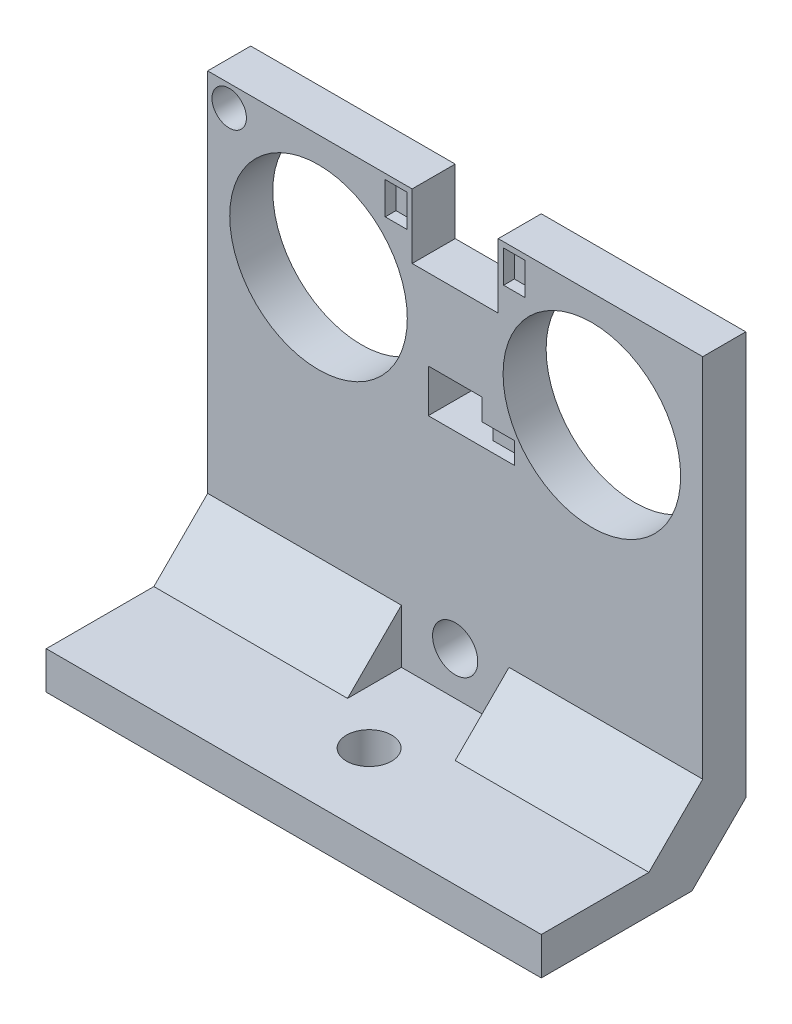
SolidWorks part; units mm, degrees
material "ABS"
ref_plane "前基準面" through (0, 0, 0) normal (0, 0, 1) x (1, 0, 0)
ref_plane "上基準面" through (0, 0, 0) normal (0, 1, 0) x (1, 0, 0)
ref_plane "右基準面" through (0, 0, 0) normal (1, 0, 0) x (0, 0, -1)
sketch "草圖1" plane through (0, 0, 0) normal (0, 0, 1) x (1, 0, 0)
  line L1 (-23, -10) -> (23, -10)
  line L2 (-23, -10) -> (-23, 10)
  line L3 (-23, 10) -> (23, 10)
  line L4 (23, -10) -> (23, 10)
  line L5 (-23, -10) -> (23, 10) construction
  line L6 (-23, 10) -> (23, -10) construction
  point P0 (0, 0)
  dimension "D1" = 46
  dimension "D2" = 20
extrude "填料-伸長1" add sketch "草圖1" along normal blind 4
sketch "草圖2" plane through (0, 0, 4) normal (0, 0, 1) x (1, 0, 0)
  line L0 (-12.7, -0.65) -> (12.7, -0.65) construction
  line L1 (23, 10) -> (-23, 10) construction
  circle A0 centre (-12.7, -0.65) radius 8.25
  circle A1 centre (12.7, -0.65) radius 8.25
  point P4 (0, -0.65)
  dimension "D1" = 25.4
  dimension "D2" = 16.5
  dimension "D3" = 10.65
extrude "除料-伸長1" cut sketch "草圖2" against normal through all
sketch "草圖3" plane through (0, 0, 4) normal (0, 0, 1) x (1, 0, 0)
  line L0 (0, 0) -> (0, 7) construction
  line L1 (23, 10) -> (-23, 10) construction
  line L2 (-4, 4) -> (4, 4)
  line L3 (-4, 4) -> (-4, 10)
  line L4 (-4, 10) -> (4, 10)
  line L5 (4, 4) -> (4, 10)
  line L6 (-4, 4) -> (4, 10) construction
  line L7 (-4, 10) -> (4, 4) construction
  dimension "D1" = 8
  dimension "D2" = 6
extrude "除料-伸長2" cut sketch "草圖3" against normal through all
sketch "草圖4" plane through (0, 0, 4) normal (0, 0, 1) x (1, 0, 0)
  line L0 (0, 0) -> (0, -5.5) construction
  line L2 (-2.5, -3.5) -> (2.5, -3.5)
  line L3 (-2.5, -3.5) -> (-2.5, -7.5)
  line L4 (-2.5, -7.5) -> (2.5, -7.5)
  line L5 (2.5, -3.5) -> (2.5, -7.5)
  line L6 (-2.5, -3.5) -> (2.5, -7.5) construction
  line L7 (-2.5, -7.5) -> (2.5, -3.5) construction
  dimension "D1" = 5
  dimension "D2" = 4
  dimension "D3" = 5.5
extrude "除料-伸長3" cut sketch "草圖4" against normal through all
sketch "草圖5" plane through (0, 0, 4) normal (0, 0, 1) x (1, 0, 0)
  line L0 (0, 0) -> (0, 8) construction
  line L1 (2.5, -7.5) -> (5.5, -7.5)
  line L2 (2.5, -7.5) -> (2.5, -5.5)
  line L3 (2.5, -5.5) -> (5.5, -5.5)
  line L4 (5.5, -7.5) -> (5.5, -5.5)
  line L5 (-5.5, 8) -> (5.5, 8) construction
  line L6 (23, 10) -> (4, 10) construction
  line L7 (-4.5, 9.5) -> (-6.5, 9.5)
  line L8 (-4.5, 9.5) -> (-4.5, 6.5)
  line L9 (-4.5, 6.5) -> (-6.5, 6.5)
  line L10 (-6.5, 9.5) -> (-6.5, 6.5)
  line L11 (-4.5, 9.5) -> (-6.5, 6.5) construction
  line L12 (-4.5, 6.5) -> (-6.5, 9.5) construction
  line L13 (6.5, 9.5) -> (4.5, 9.5)
  line L14 (6.5, 9.5) -> (6.5, 6.5)
  line L15 (6.5, 6.5) -> (4.5, 6.5)
  line L16 (4.5, 9.5) -> (4.5, 6.5)
  line L17 (6.5, 9.5) -> (4.5, 6.5) construction
  line L18 (6.5, 6.5) -> (4.5, 9.5) construction
  point P10 (0, 8)
  dimension "D1" = 2
  dimension "D2" = 3
  dimension "D3" = 2
  dimension "D4" = 3
  dimension "D5" = 11
  dimension "D6" = 0.5
extrude "除料-伸長4" cut sketch "草圖5" against normal blind 1
sketch "草圖6" plane through (0, -10, 0) normal (0, -1, 0) x (1, 0, 0)
  line L1 (-23, 4) -> (23, 4)
  line L2 (-23, 4) -> (-23, 0)
  line L3 (-23, 0) -> (23, 0)
  line L4 (23, 4) -> (23, 0)
extrude "填料-伸長2" add sketch "草圖6" along normal blind 22.5
sketch "草圖8" plane through (-23, 0, 0) normal (-1, 0, 0) x (0, 0, 1)
  line L0 (4, -32.5) -> (19, -32.5)
  line L1 (19, -32.5) -> (19, -29)
  line L2 (19, -29) -> (4, -29)
  line L3 (4, 10) -> (4, -32.5) construction
  line L4 (4, -29) -> (4, -32.5)
  dimension "D1" = 3.5
  dimension "D2" = 15
extrude "填料-伸長4" add sketch "草圖8" against normal blind 46
chamfer "導角3" distance 5 angle 45 2 edges at (0, -32.5, 0) (0, -29, 4)
sketch "草圖9" plane through (0, -29, 0) normal (0, 1, 0) x (1, 0, 0)
  line L0 (0, -4) -> (0, -19) construction
  line L1 (23, -4) -> (-23, -4) construction
  line L2 (23, -19) -> (-23, -19) construction
  circle A0 centre (0, -12) radius 2.1
  dimension "D1" = 4.2
  dimension "D2" = 8
extrude "除料-伸長5" cut sketch "草圖9" against normal through all
sketch "草圖10" plane through (0, 0, 0) normal (0, 0, -1) x (-1, 0, 0)
  line L0 (0, -25) -> (0, -32.5) construction
  line L1 (23, -32.5) -> (-23, -32.5) construction
  circle A0 centre (0, -25) radius 2.1
  dimension "D2" = 4.2
  dimension "D1" = 7.5
extrude "除料-伸長6" cut sketch "草圖10" against normal through all
sketch "草圖13" plane through (0, 0, 4) normal (0, 0, 1) x (1, 0, 0)
  line L0 (23, -29) -> (-23, -29) construction
  line L1 (-5, -21) -> (5, -21)
  line L2 (-5, -21) -> (-5, -29)
  line L3 (-5, -29) -> (5, -29)
  line L4 (5, -21) -> (5, -29)
  line L5 (-5, -21) -> (5, -29) construction
  line L6 (-5, -29) -> (5, -21) construction
  point P0 (0, -25)
  dimension "D1" = 10
extrude "除料-伸長9" cut sketch "草圖13" along normal blind 46
sketch "草圖14" plane through (0, 0, 4) normal (0, 0, 1) x (1, 0, 0)
  line L0 (-21, 8) -> (-23, 8) construction
  line L1 (-23, 10) -> (-23, -24) construction
  line L2 (-4, 10) -> (-23, 10) construction
  circle A0 centre (-21, 8) radius 1.6
  dimension "D1" = 3.2
  dimension "D2" = 2
  dimension "D3" = 2
extrude "除料-伸長10" cut sketch "草圖14" against normal blind 46
